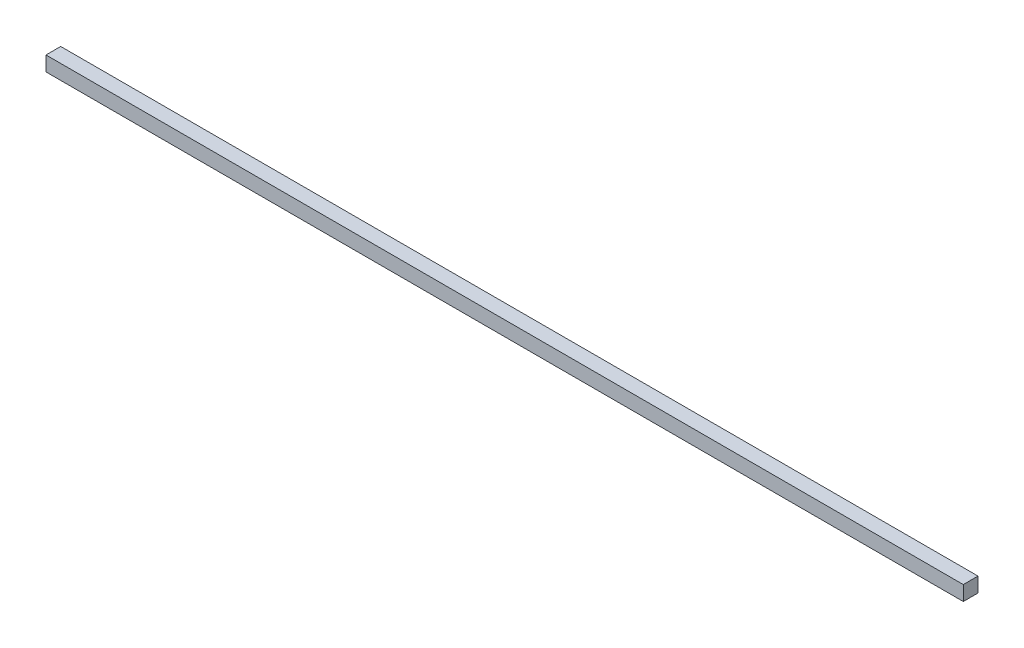
SolidWorks part; units mm, degrees
ref_plane "Front Plane" through (0, 0, 0) normal (0, 0, 1) x (1, 0, 0)
ref_plane "Top Plane" through (0, 0, 0) normal (0, 1, 0) x (1, 0, 0)
ref_plane "Right Plane" through (0, 0, 0) normal (1, 0, 0) x (0, 0, -1)
sketch "Sketch1" plane through (0, 0, 0) normal (0, 1, 0) x (1, 0, 0)
  line L1 (0, 0) -> (187, 0)
  line L2 (0, 0) -> (0, 3)
  line L3 (0, 3) -> (187, 3)
  line L4 (187, 0) -> (187, 3)
  dimension "D1" = 3
  dimension "D2" = 187
extrude "Boss-Extrude1" add sketch "Sketch1" along normal blind 3
